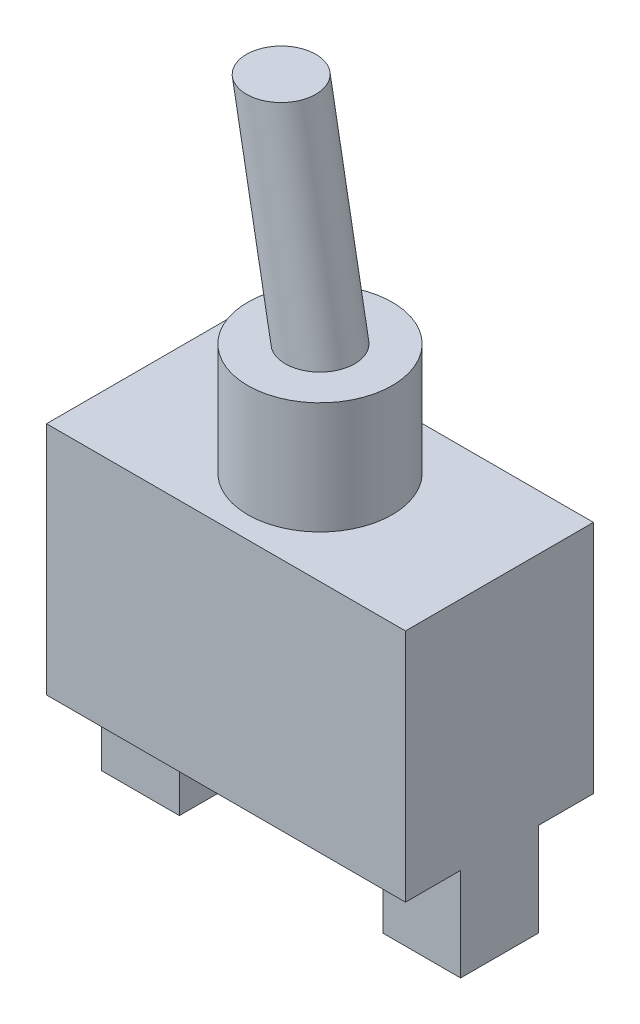
SolidWorks part; units mm, degrees
ref_plane "Front Plane" through (0, 0, 0) normal (0, 0, 1) x (1, 0, 0)
ref_plane "Top Plane" through (0, 0, 0) normal (0, 1, 0) x (1, 0, 0)
ref_plane "Right Plane" through (0, 0, 0) normal (1, 0, 0) x (0, 0, -1)
sketch "Sketch1" plane through (0, 0, 0) normal (0, 1, 0) x (1, 0, 0)
  line L1 (-14.6685, -7.6835) -> (14.6685, -7.6835)
  line L2 (-14.6685, -7.6835) -> (-14.6685, 7.6835)
  line L3 (-14.6685, 7.6835) -> (14.6685, 7.6835)
  line L4 (14.6685, -7.6835) -> (14.6685, 7.6835)
  line L5 (-14.6685, -7.6835) -> (14.6685, 7.6835) construction
  line L6 (-14.6685, 7.6835) -> (14.6685, -7.6835) construction
  point P0 (0, 0)
  dimension "D1" = 15.367
  dimension "D2" = 29.337
extrude "Boss-Extrude1" add sketch "Sketch1" along normal blind 19.2024
sketch "Sketch2" plane through (0, 19.2024, 0) normal (0, 1, 0) x (1, 0, 0)
  circle A0 centre (0, 0) radius 5.9055
  dimension "D1" = 11.811
extrude "Boss-Extrude2" add sketch "Sketch2" along normal blind 9.144
sketch "Sketch3" plane through (0, 0, 0) normal (0, -1, 0) x (1, 0, 0)
  line L0 (-14.6685, -7.6835) -> (-14.6685, 7.6835) construction
  line L1 (-14.6685, 3.175) -> (-8.3185, 3.175)
  line L2 (-14.6685, 3.175) -> (-14.6685, -3.175)
  line L3 (-14.6685, -3.175) -> (-8.3185, -3.175)
  line L4 (-8.3185, 3.175) -> (-8.3185, -3.175)
  line L5 (0, -8.4519) -> (0, 8.4519) construction
  line L6 (14.6685, -3.175) -> (8.3185, -3.175)
  line L7 (8.3185, 3.175) -> (8.3185, -3.175)
  line L8 (14.6685, 3.175) -> (8.3185, 3.175)
  line L9 (14.6685, 3.175) -> (14.6685, -3.175)
  point P6 (-14.6685, 0)
  dimension "D1" = 6.35
  dimension "D2" = 6.35
extrude "Boss-Extrude3" add sketch "Sketch3" along normal blind 7.62
sketch "Sketch4" plane through (0, 28.3464, 0) normal (0, 1, 0) x (1, 0, 0)
  circle A0 centre (0, 0) radius 2.8321
  dimension "D1" = 5.6642
sketch "Sketch5" plane through (0, 0, 0) normal (0, 0, 1) x (1, 0, 0)
  line L0 (0, 28.3464) -> (-3.175, 45.8406)
  dimension "D1" = 17.78
  dimension "D2" = 3.175
sweep "Sweep1" add profiles "Sketch4" path "Sketch5"
